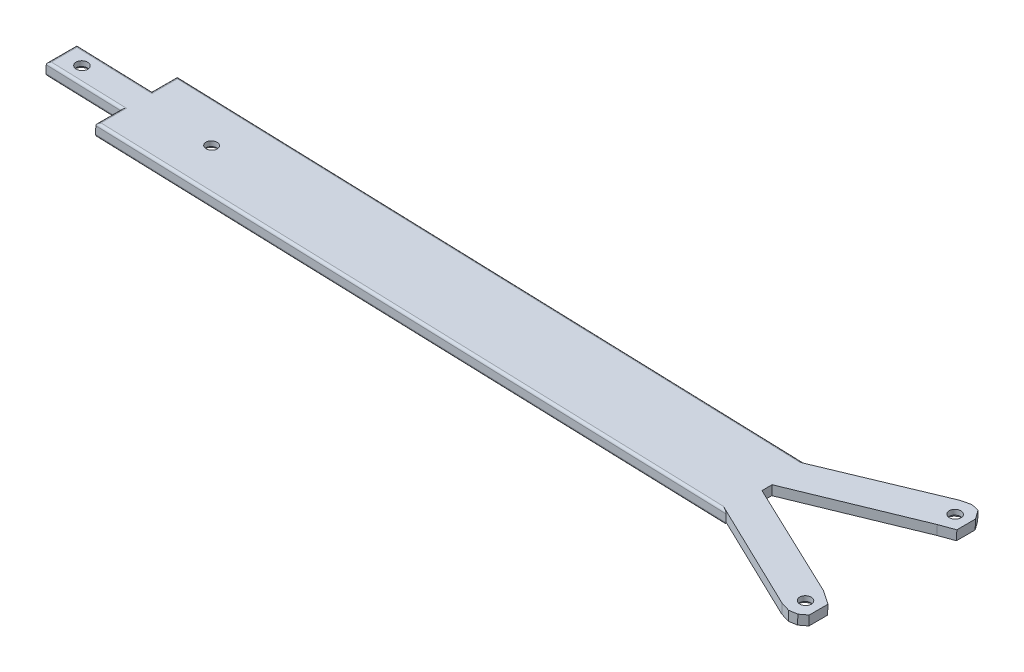
SolidWorks part; units mm, degrees
ref_plane "Front Plane" through (0, 0, 0) normal (0, 0, 1) x (1, 0, 0)
ref_plane "Top Plane" through (0, 0, 0) normal (0, 1, 0) x (1, 0, 0)
ref_plane "Right Plane" through (0, 0, 0) normal (1, 0, 0) x (0, 0, -1)
sketch "Sketch1" plane through (0.1422, 4.2506, 0) normal (-0.0334, -0.9994, 0) x (0.9994, -0.0334, 0)
  line L1 (11.4434, 116.2) -> (14.1674, 118.021)
  line L2 (-10.8326, 113) -> (9.6396, 122.5)
  line L3 (12.9434, 122.7) -> (14.1674, 121.6881)
  line L4 (-149.5566, 108) -> (-134.8067, 108)
  line L5 (-149.5566, 102) -> (-134.8067, 102)
  line L6 (-149.5566, 102) -> (-149.5566, 108)
  line L7 (-134.8067, 99.6499) -> (-134.8067, 110.3499) construction
  line L8 (-134.8067, 108) -> (-134.8067, 113)
  line L9 (-134.8067, 113) -> (-10.8326, 113)
  line L10 (-134.8067, 102) -> (-134.8067, 97)
  line L11 (-134.8067, 97) -> (-10.8326, 97)
  line L15 (14.1674, 89.021) -> (14.1674, 92.6881) construction
  line L19 (14.1674, 118.021) -> (14.1674, 121.6881) construction
  line L20 (11.4434, 87) -> (9.6434, 87.5)
  line L21 (12.9434, 87.3) -> (11.4434, 87)
  line L22 (11.4434, 93.8) -> (14.1674, 92.6881)
  line L23 (14.1674, 89.021) -> (14.1674, 92.6881)
  line L25 (9.6396, 122.5) -> (11.4434, 123)
  line L26 (11.4434, 123) -> (12.9434, 122.7)
  line L27 (14.1674, 118.021) -> (14.1674, 121.6881)
  line L29 (11.4434, 116.2) -> (-10.8326, 106)
  line L31 (14.1674, 89.021) -> (12.9434, 87.3)
  line L32 (9.6434, 87.5) -> (-10.8326, 97)
  line L33 (11.4434, 93.8) -> (-10.8326, 104)
  line L34 (-10.8326, 106) -> (-10.8326, 104)
  circle A0 centre (11.4434, 119.7) radius 1.15 construction
  circle A1 centre (11.4434, 90.3) radius 1.15 construction
  circle A2 centre (-145.5566, 105) radius 1.15 construction
  circle A3 centre (-120.0566, 105) radius 1.1 construction
  circle A4 centre (11.4434, 119.7) radius 1.15
  circle A5 centre (11.4434, 90.3) radius 1.15
  circle A6 centre (-145.5566, 105) radius 1.15
  circle A7 centre (-120.0566, 105) radius 1.1
  point P0 (14.1674, 119.8546)
  dimension "D1" = 3
  dimension "D2" = 3
  dimension "D3" = 16
  dimension "D4" = 8
  dimension "D5" = 25
  dimension "D6" = 4
  dimension "D7" = 1.8039
  dimension "D8" = 3.5
  dimension "D9" = 2
  dimension "D10" = 2.8
  dimension "D11" = 0.5
  dimension "D12" = 1.5
  dimension "D13" = 3
  dimension "D14" = 3.5
  dimension "D15" = 1.8
  dimension "D16" = 2.8
  dimension "D17" = 0.5
  dimension "D18" = 1.5
  dimension "D19" = 7
  dimension "D20" = 3
extrude "Boss-Extrude1" add sketch "Sketch1" along normal blind 2.5
sketch "Sketch2" plane through (0.0586, 1.752, 0) normal (-0.0334, -0.9994, 0) x (0.9994, -0.0334, 0)
  circle A0 centre (-145.5566, 105) radius 2.1
  circle A1 centre (-120.0566, 105) radius 2.1
  circle A2 centre (11.4434, 119.7) radius 2.1
  circle A3 centre (11.4434, 90.3) radius 2.1
  dimension "D1" = 4.2
extrude "Cut-Extrude1" cut sketch "Sketch2" against normal blind 1.5
sketch "Sketch3" plane through (0.0586, 1.752, 0) normal (-0.0334, -0.9994, 0) x (0.9994, -0.0334, 0)
  line L0 (-10.8326, 113) -> (-134.8067, 113) construction
  line L1 (-113.8345, 108) -> (-18.3297, 108)
  line L2 (-113.8345, 108) -> (-113.8345, 102)
  line L3 (-113.8345, 102) -> (-18.3297, 102)
  line L4 (-18.3297, 108) -> (-18.3297, 102)
  line L5 (-134.8067, 97) -> (-10.8326, 97) construction
  dimension "D1" = 5
  dimension "D2" = 5
extrude "Boss-Extrude2" add sketch "Sketch3" along normal blind 1.5
fillet "Fillet1" radius 0.5 8 edges at (-65.9866, 3.9616, 108) (-113.7122, 5.5583, 105) (-18.2609, 2.3649, 105) (-65.9866, 3.9616, 102) (-18.311, 0.8657, 105) (-66.0367, 2.4625, 108) (-113.7624, 4.0592, 105) (-66.0367, 2.4625, 102)
fillet "Fillet2" radius 0.5 14 edges at (-141.9599, 9.0048, 102) (-149.3307, 9.2514, 105) (-141.9599, 9.0048, 108) (-134.5891, 8.7582, 110.5) (-134.5891, 8.7582, 99.5) (-72.6367, 6.6855, 113) (-72.6367, 6.6855, 97) (-134.6727, 6.2596, 99.5) (-72.7203, 4.1869, 97) (-72.7203, 4.1869, 113) (-134.6727, 6.2596, 110.5) (-142.0435, 6.5062, 108) (-149.4143, 6.7528, 105) (-142.0435, 6.5062, 102)
sketch "Sketch4" plane through (0.0586, 1.752, 0) normal (-0.0334, -0.9994, 0) x (0.9994, -0.0334, 0)
  line L0 (14.1674, 118.021) -> (14.1674, 121.6881) construction
  line L1 (14.1674, 89.021) -> (14.1674, 92.6881) construction
  line L2 (14.1674, 118.021) -> (14.1674, 121.6881)
  line L3 (14.1674, 89.021) -> (14.1674, 92.6881)
  line L5 (16.7035, 123.9672) -> (18.8636, 123.9672)
  line L6 (16.7035, 123.9672) -> (16.7035, 85.5707)
  line L7 (16.7035, 85.5707) -> (18.8636, 85.5707)
  line L8 (18.8636, 123.9672) -> (18.8636, 85.5707)
  circle M11 centre (11.4434, 119.7) radius 2.1
  circle M12 centre (11.4434, 90.3) radius 2.1
  line M16 (11.4434, 87) -> (12.9434, 87.3)
  line M17 (12.9434, 87.3) -> (14.1674, 89.021)
  line M18 (14.1674, 89.021) -> (14.1674, 92.6881)
  line M19 (14.1674, 92.6881) -> (11.4434, 93.8)
  line M23 (11.4434, 116.2) -> (14.1674, 118.021)
  line M24 (14.1674, 118.021) -> (14.1674, 121.6881)
  line M25 (14.1674, 121.6881) -> (12.9434, 122.7)
  line M26 (12.9434, 122.7) -> (11.4434, 123)
extrude "Cut-Extrude2" cut sketch "Sketch4" against normal blind 0.6 contours L6 M19 M12 M16 M17 M18 | L6 M26 M11 M23 M24 M25
